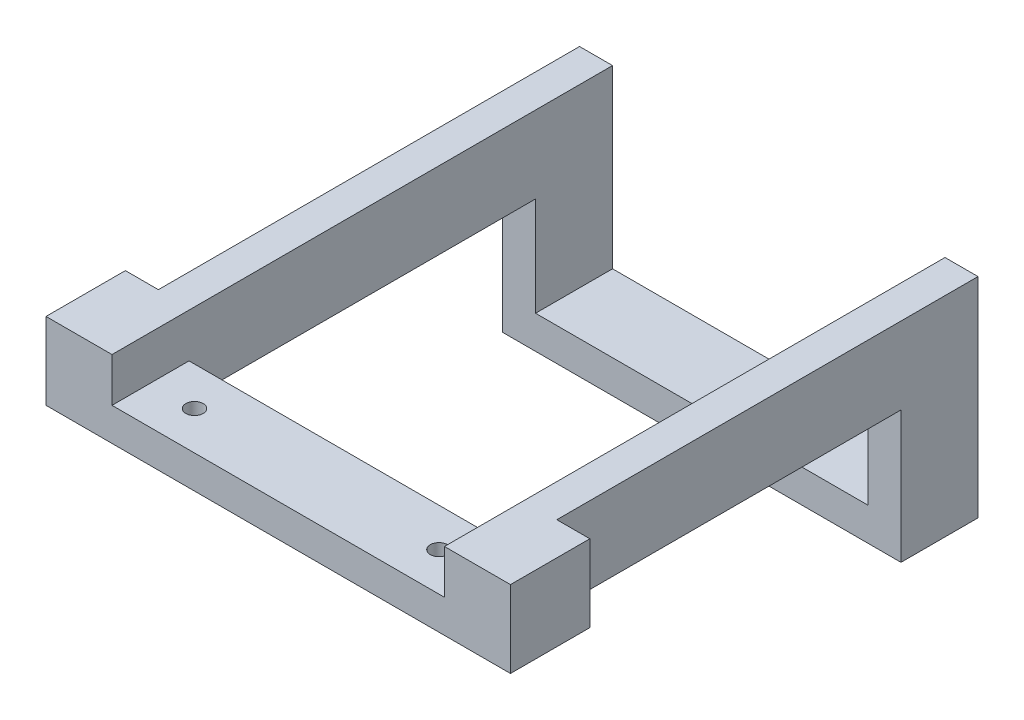
SolidWorks part; units mm, degrees
ref_plane "Front Plane" through (0, 0, 0) normal (0, 0, 1) x (1, 0, 0)
ref_plane "Top Plane" through (0, 0, 0) normal (0, 1, 0) x (1, 0, 0)
ref_plane "Right Plane" through (0, 0, 0) normal (1, 0, 0) x (0, 0, -1)
sketch "Sketch1" plane through (0, 0, 0) normal (0, 1, 0) x (1, 0, 0)
  line L1 (230, -44.45) -> (-230, -44.45)
  line L2 (230, -44.45) -> (230, 44.45)
  line L3 (230, 44.45) -> (-230, 44.45)
  line L4 (-230, -44.45) -> (-230, 44.45)
  line L5 (230, -44.45) -> (-230, 44.45) construction
  line L6 (230, 44.45) -> (-230, -44.45) construction
  point P0 (0, 0)
  dimension "D1" = 460
  dimension "D2" = 88.9
extrude "Boss-Extrude1" add sketch "Sketch1" along normal blind 38.1
sketch "Sketch2" plane through (0, 38.1, 0) normal (0, 1, 0) x (1, 0, 0)
  line L0 (-230, -44.45) -> (230, -44.45) construction
  line L1 (-230, 44.45) -> (-191.9, 44.45)
  line L2 (-230, 44.45) -> (-230, -44.45)
  line L3 (-230, -44.45) -> (-191.9, -44.45)
  line L4 (-191.9, 44.45) -> (-191.9, -44.45)
  line L6 (230, 44.45) -> (191.9, 44.45)
  line L7 (230, 44.45) -> (230, -44.45)
  line L8 (230, -44.45) -> (191.9, -44.45)
  line L9 (191.9, 44.45) -> (191.9, -44.45)
  dimension "D1" = 38.1
  dimension "D2" = 38.1
extrude "Boss-Extrude2" add sketch "Sketch2" along normal blind 910
sketch "Sketch3" plane through (0, 0, -44.45) normal (0, 0, -1) x (-1, 0, 0)
  line L0 (230, 948.1) -> (191.9, 948.1)
  line L1 (230, 948.1) -> (230, 1037)
  line L2 (191.9, 948.1) -> (191.9, 1037)
  line L3 (230, 1037) -> (191.9, 1037)
  line L4 (-191.9, 948.1) -> (-230, 948.1)
  line L5 (-191.9, 948.1) -> (-191.9, 1037)
  line L6 (-230, 948.1) -> (-230, 1037)
  line L7 (-191.9, 1037) -> (-230, 1037)
  dimension "D1" = 88.9
extrude "Boss-Extrude3" add sketch "Sketch3" against normal blind 577.85
sketch "Sketch4" plane through (0, 948.1, 0) normal (0, -1, 0) x (1, 0, 0)
  line L11 (-230, 533.4) -> (-268.1, 533.4)
  line L12 (-230, 533.4) -> (-230, 441.7687)
  line L13 (-230, 441.7687) -> (-268.1, 441.7687)
  line L14 (-268.1, 533.4) -> (-268.1, 441.7687)
  line L15 (230, 533.4) -> (268.1, 533.4)
  line L16 (230, 533.4) -> (230, 441.7687)
  line L17 (230, 441.7687) -> (268.1, 441.7687)
  line L18 (268.1, 533.4) -> (268.1, 441.7687)
  point P9 (0, 0)
  point P10 (0, 0)
  point P12 (-268.1, 533.4)
  line M7 (-230, 533.4) -> (-230, 44.45)
  dimension "D1" = 38.1
extrude "Boss-Extrude4" add sketch "Sketch4" along normal blind 615 and the other way up to surface (88.9 mm away) contours L11 L14 L13 M7 | L18 L17 L16 L15 other way up to face at (-210.95, 1037, 244.475)
sketch "Sketch5" plane through (230, 0, 0) normal (-1, 0, 0) x (0, 0, 1)
  line L0 (533.4, 948.1) -> (533.4, 333.1) construction
  line L1 (441.7687, 333.1) -> (533.4, 333.1)
  line L2 (441.7687, 333.1) -> (441.7687, 371.2)
  line L3 (441.7687, 371.2) -> (533.4, 371.2)
  line L4 (533.4, 333.1) -> (533.4, 371.2)
  dimension "D1" = 38.1
extrude "Boss-Extrude5" add sketch "Sketch5" along normal up to surface (460 mm away) up to face at (-230, 640.6, 487.5844)
sketch "Sketch7" plane through (0, 0, 533.4) normal (0, 0, 1) x (1, 0, 0)
  line L0 (268.1, 1037) -> (268.1, 333.1) construction
  line L10 (268.1, 795.7) -> (-577.3673, 795.7)
  line L13 (268.1, 795.7) -> (268.1, -246.2731)
  line L14 (268.1, -246.2731) -> (-577.3673, -246.2731)
  line L15 (-577.3673, 795.7) -> (-577.3673, -246.2731)
  line L16 (-268.1, 1037) -> (-268.1, 333.1) construction
  line L17 (268.1, 795.7) -> (230, 795.7)
  line L18 (268.1, 795.7) -> (268.1, 948.1)
  line L19 (268.1, 948.1) -> (230, 948.1)
  line L20 (230, 795.7) -> (230, 948.1)
  line L26 (-230, 948.1) -> (-268.1, 948.1)
  line L27 (-230, 948.1) -> (-230, 795.7)
  line L28 (-230, 795.7) -> (-268.1, 795.7)
  line L29 (-268.1, 948.1) -> (-268.1, 795.7)
  line M6 (-268.1, 1037) -> (-268.1, 333.1)
  line M7 (-268.1, 333.1) -> (268.1, 333.1)
  line M8 (268.1, 333.1) -> (268.1, 1037)
  line M12 (230, 948.1) -> (230, 371.2)
  line M13 (230, 371.2) -> (-230, 371.2)
  line M14 (-230, 371.2) -> (-230, 948.1)
  dimension "D1" = 152.4
extrude "Cut-Extrude1" cut sketch "Sketch7" against normal up to surface (577.85 mm away) contours L10 M12 M14 M13 | L10 L15 L14 L13 M7 M6 | L10 M8 M12 M13 M14 M6 M7 | L19 L10 M8 M12 | L26 L10 M14 M6 up to face at (0, 528.025, -44.45)
sketch "Sketch8" plane through (-191.9, 0, 0) normal (1, 0, 0) x (0, 0, -1)
  line L0 (-44.45, 948.1) -> (-44.45, 795.7) construction
  line L1 (44.45, 795.7) -> (-44.45, 795.7)
  line L2 (44.45, 795.7) -> (44.45, 833.8)
  line L3 (44.45, 833.8) -> (-44.45, 833.8)
  line L4 (-44.45, 795.7) -> (-44.45, 833.8)
  line L6 (-533.4, 948.1) -> (-444.5, 948.1)
  line L7 (-533.4, 948.1) -> (-533.4, 986.2)
  line L8 (-533.4, 986.2) -> (-444.5, 986.2)
  line L9 (-444.5, 948.1) -> (-444.5, 986.2)
  dimension "D1" = 38.1
  dimension "D2" = 88.9
  dimension "D3" = 38.1
extrude "Boss-Extrude6" add sketch "Sketch8" along normal up to surface (383.8 mm away) up to face at (191.9, 926.9333, 177.8)
sketch "Sketch9" plane through (0, 795.7, 0) normal (0, -1, 0) x (1, 0, 0)
  line L0 (-230, 0) -> (230, 0) construction
  line L1 (-230, -44.45) -> (-230, 44.45) construction
  line L2 (230, -44.45) -> (230, 44.45) construction
  line L3 (0, 44.45) -> (0, -44.45) construction
  line L4 (-230, 44.45) -> (230, 44.45) construction
  line L5 (-230, -44.45) -> (230, -44.45) construction
  circle A0 centre (0, 0) radius 10
  dimension "D1" = 20
sketch "Sketch10" plane through (0, 948.1, 0) normal (0, -1, 0) x (1, 0, 0)
  line L0 (141.1, 488.95) -> (-141.1, 488.95) construction
  line L3 (0, 533.4) -> (0, 444.5) construction
  line L4 (268.1, 533.4) -> (-268.1, 533.4) construction
  line L5 (191.9, 444.5) -> (-191.9, 444.5) construction
  circle A0 centre (-141.1, 488.95) radius 10
  circle A1 centre (141.1, 488.95) radius 10
  point P3 (0, 488.95)
  dimension "D2" = 20
  dimension "D1" = 282.2
extrude "Cut-Extrude2" cut sketch "Sketch10" against normal up to surface (38.1 mm away) up to face at (0, 986.2, 488.95)
extrude "Cut-Extrude3" cut sketch "Sketch9" against normal up to surface (38.1 mm away) up to face at (0, 833.8, 0)
